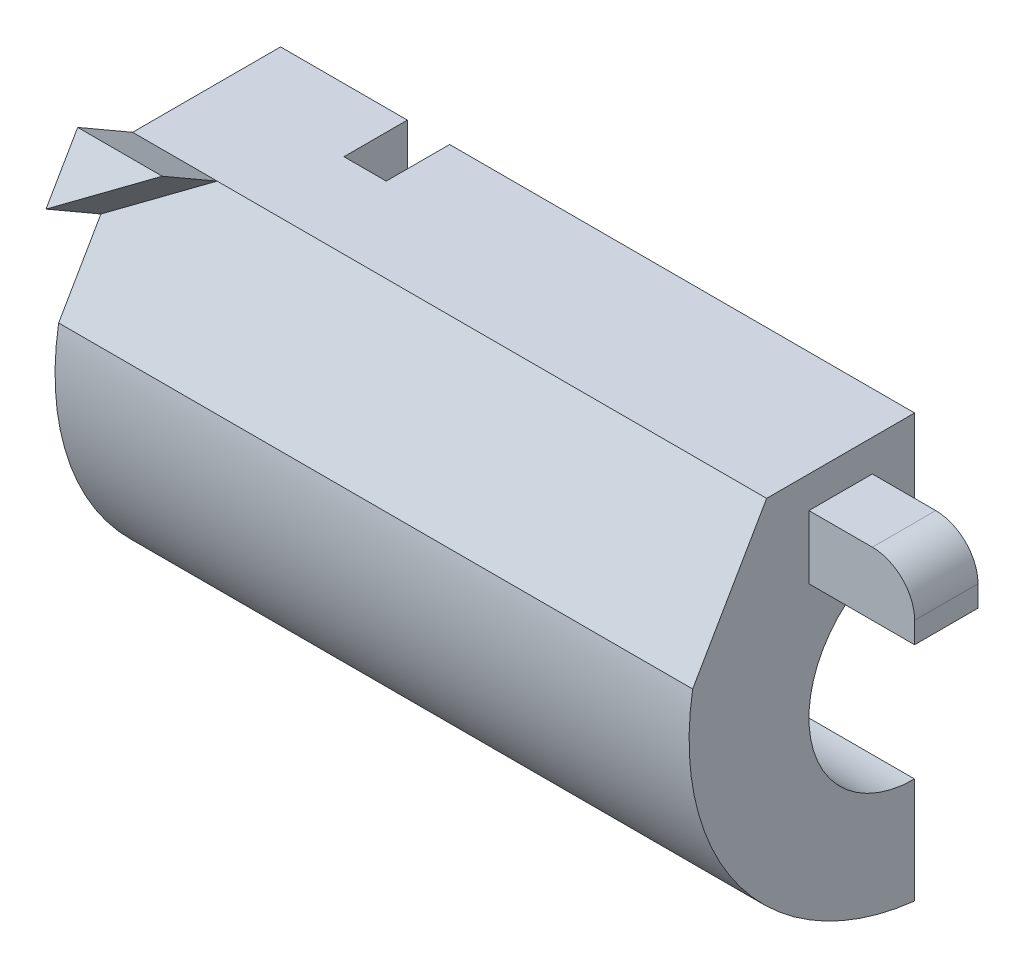
SolidWorks part; units mm, degrees
material "AISI 1020"
ref_plane "Front Plane" through (0, 0, 0) normal (0, 0, 1) x (1, 0, 0)
ref_plane "Top Plane" through (0, 0, 0) normal (0, 1, 0) x (1, 0, 0)
ref_plane "Right Plane" through (0, 0, 0) normal (1, 0, 0) x (0, 0, -1)
sketch "Sketch2" plane through (0, 0, 0) normal (1, 0, 0) x (0, 0, -1)
  line L0 (0, -10) -> (0, 10)
  line L1 (0, 10) -> (-7, 10)
  line L2 (-7, 10) -> (-10.5, 3.9378)
  arc A0 (-10.5, 3.9378) -> (0, -10) centre (1.3302, 1.926) ccw
extrude "Boss-Extrude1" add sketch "Sketch2" against normal blind 30
sketch "Sketch3" plane through (0, 0, 0) normal (1, 0, 0) x (0, 0, -1)
  line L0 (0, -10) -> (0, 10) construction
  line L1 (0, -5) -> (0, 5)
  arc A0 (0, -5) -> (0, 5) centre (0, 0) cw
  dimension "D1" = 5
  dimension "D2" = 5
  dimension "D3" = 5
extrude "Cut-Extrude1" cut sketch "Sketch3" against normal blind 10
sketch "Sketch4" plane through (-30, 0, 0) normal (-1, 0, 0) x (0, 0, 1)
  line L0 (0, -10) -> (0, 10) construction
  line L1 (0, -3) -> (0, 3)
  arc A0 (0, -3) -> (0, 3) centre (0, 0) ccw
  dimension "D1" = 3
  dimension "D2" = 7
  dimension "D3" = 7
extrude "Cut-Extrude2" cut sketch "Sketch4" against normal blind 10
sketch "Sketch5" plane through (0, 0, 0) normal (1, 0, 0) x (0, 0, -1)
  line L0 (0, 5) -> (0, 10) construction
  line L1 (-5, 8.5) -> (-2, 8.5)
  line L2 (-5, 8.5) -> (-5, 5.5)
  line L3 (-5, 5.5) -> (-2, 5.5)
  line L4 (-2, 8.5) -> (-2, 5.5)
  line L5 (0, 10) -> (-7, 10) construction
  dimension "D1" = 3
  dimension "D2" = 3
  dimension "D3" = 2
  dimension "D4" = 1.5
extrude "Boss-Extrude2" add sketch "Sketch5" along normal blind 5
fillet "Fillet2" radius 2 1 edges at (5, 8.5, 3.5)
sketch "Sketch7" plane through (0, 10, 0) normal (0, 1, 0) x (1, 0, 0)
  line L0 (-30, 0) -> (0, 0) construction
  line L1 (-24, 0) -> (-22, 0)
  line L2 (-24, 0) -> (-24, -3)
  line L3 (-24, -3) -> (-22, -3)
  line L4 (-22, 0) -> (-22, -3)
  line L5 (-30, 0) -> (-30, -7) construction
  dimension "D1" = 3
  dimension "D2" = 2
  dimension "D3" = 6
extrude "Cut-Extrude3" cut sketch "Sketch7" against normal blind 8.5
sketch "Sketch8" plane through (0, 5.5311, 9.5801) normal (0, 0.5, 0.866) x (1, 0, 0)
  line L0 (-30, 2.1603) -> (-26, 5.1603)
  line L1 (-30, 5.1603) -> (-30, -1.8397) construction
  line L2 (-30, 5.1603) -> (0, 5.1603) construction
  line L3 (-26, 5.1603) -> (-30, 5.1603)
  line L4 (-30, 5.1603) -> (-30, 2.1603)
  dimension "D1" = 3
  dimension "D2" = 5
extrude "Boss-Extrude3" add sketch "Sketch8" along normal blind 3
equation "\"a\"= 120"
equation "\"D5@Sketch2\"=\"a\""
